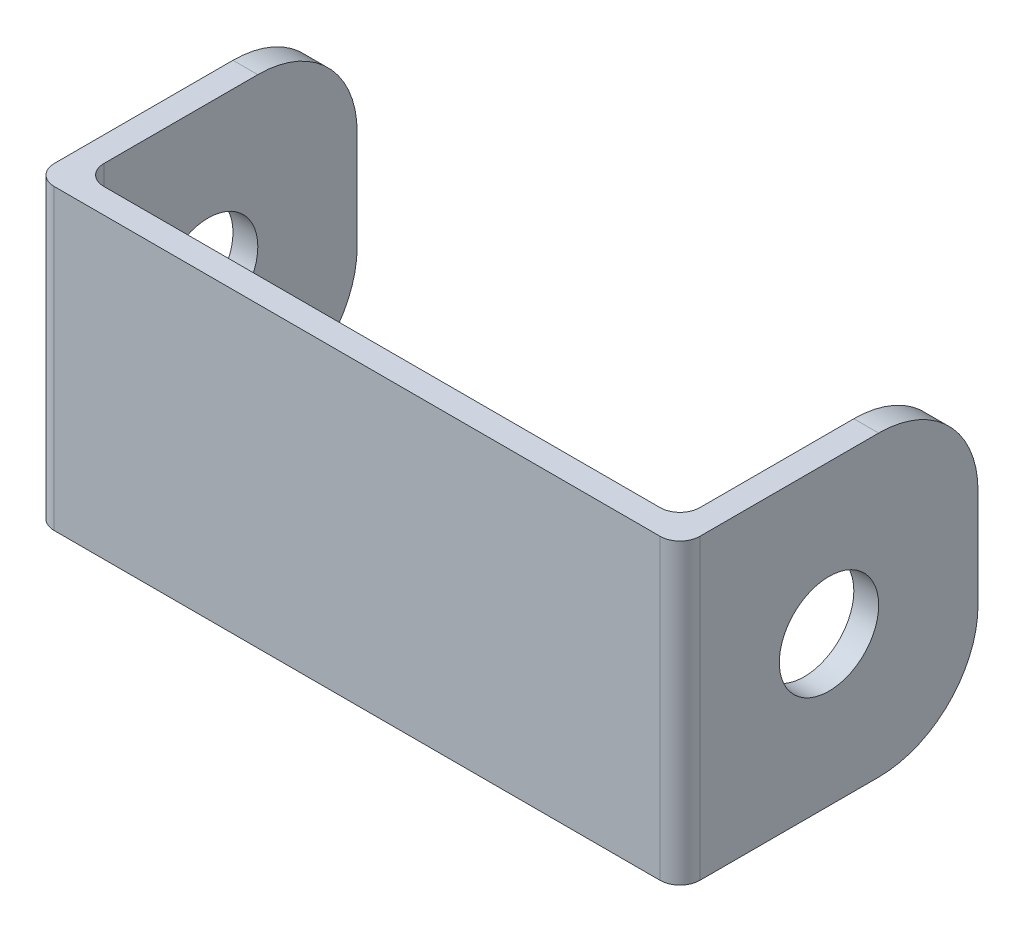
SolidWorks part; units mm, degrees
ref_plane "Front Plane" through (0, 0, 0) normal (0, 0, 1) x (1, 0, 0)
ref_plane "Top Plane" through (0, 0, 0) normal (0, 1, 0) x (1, 0, 0)
ref_plane "Right Plane" through (0, 0, 0) normal (1, 0, 0) x (0, 0, -1)
sketch "Sketch1" plane through (0, 0, 0) normal (0, 1, 0) x (1, 0, 0)
  line L0 (-11.9063, 27.9797) -> (-11.9063, -10.1203)
  line L1 (-11.9063, -10.1203) -> (70.6437, -10.1203)
  line L2 (70.6437, -10.1203) -> (70.6437, 27.9797)
  line L3 (70.6437, 27.9797) -> (67.4687, 27.9797)
  line L4 (67.4687, 27.9797) -> (67.4688, -6.9453)
  line L5 (67.4688, -6.9453) -> (-8.7313, -6.9453)
  line L6 (-8.7313, -6.9453) -> (-8.7313, 27.9797)
  line L7 (-8.7313, 27.9797) -> (-11.9063, 27.9797)
  dimension "D1" = 3.175
  dimension "D2" = 3.175
  dimension "D3" = 76.2
  dimension "D4" = 38.1
extrude "Boss-Extrude1" add sketch "Sketch1" along normal blind 38.1
sketch "Sketch4" plane through (70.6437, 0, 0) normal (1, 0, 0) x (0, 0, -1)
  line L0 (8.9297, 38.1) -> (8.9297, 0) construction
  line L1 (-10.1203, 19.05) -> (27.5672, 19.05) construction
  circle A0 centre (8.9297, 19.05) radius 6.35
  dimension "D1" = 12.7
extrude "Cut-Extrude1" cut sketch "Sketch4" against normal through all
fillet "Fillet1" radius 12.7 4 edges at (-10.3188, 38.1, -27.9797) (-10.3188, 0, -27.9797) (69.0562, 0, -27.9797) (69.0562, 38.1, -27.9797)
fillet "Fillet2" radius 2.54 4 edges at (70.6437, 19.05, 10.1203) (-11.9063, 19.05, 10.1203) (-8.7313, 19.05, 6.9453) (67.4688, 19.05, 6.9453)
sketch "Sketch5" plane through (0, 0, 10.1203) normal (0, 0, 1) x (1, 0, 0)
  line L0 (29.3687, 0) -> (29.3687, 38.1) construction
  line L1 (-9.3663, 0) -> (68.1037, 0) construction
  line L2 (-9.3663, 38.1) -> (68.1037, 38.1) construction
  line L3 (68.1037, 19.05) -> (-9.3663, 19.05) construction
  line L4 (68.1037, 0) -> (68.1037, 38.1) construction
  line L5 (-9.3663, 38.1) -> (-9.3663, 0) construction
